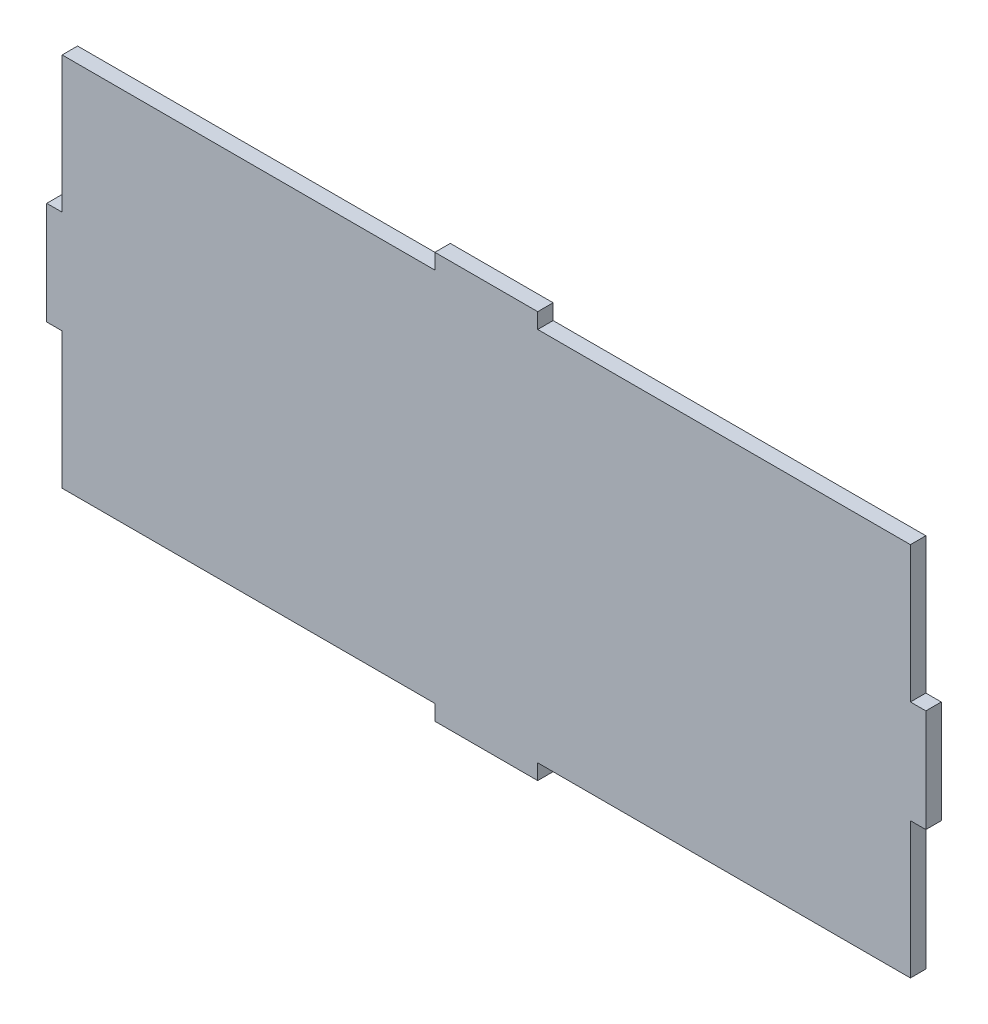
SolidWorks part; units mm, degrees
ref_plane "Plano frontal" through (0, 0, 0) normal (0, 0, 1) x (1, 0, 0)
ref_plane "Plano superior" through (0, 0, 0) normal (0, 1, 0) x (1, 0, 0)
ref_plane "Plano direito" through (0, 0, 0) normal (1, 0, 0) x (0, 0, -1)
sketch "Esboço1" plane through (0, 0, 0) normal (0, 0, 1) x (1, 0, 0)
  line L0 (-82.5, 36.5) -> (82.5, 36.5)
  line L1 (-82.5, 36.5) -> (-82.5, -36.5)
  line L2 (-82.5, -36.5) -> (82.5, -36.5)
  line L3 (82.5, 36.5) -> (82.5, -36.5)
  line L4 (-82.5, 10) -> (-85.5, 10)
  line L5 (-82.5, 10) -> (-82.5, -10)
  line L6 (-82.5, -10) -> (-85.5, -10)
  line L7 (-85.5, 10) -> (-85.5, -10)
  line L8 (-10, -36.5) -> (10, -36.5)
  line L9 (-10, -36.5) -> (-10, -39.5)
  line L10 (-10, -39.5) -> (10, -39.5)
  line L11 (10, -36.5) -> (10, -39.5)
  line L12 (10, 36.5) -> (-10, 36.5)
  line L13 (10, 36.5) -> (10, 39.5)
  line L14 (10, 39.5) -> (-10, 39.5)
  line L15 (-10, 36.5) -> (-10, 39.5)
  line L16 (82.5, 10) -> (85.5, 10)
  line L17 (82.5, 10) -> (82.5, -10)
  line L18 (82.5, -10) -> (85.5, -10)
  line L19 (85.5, 10) -> (85.5, -10)
extrude "Ressalto-extrusão1" add sketch "Esboço1" along normal blind 3 contours L3 L0 L1 L2 | L15 L0 L13 L14 | L7 L6 L5 L4 | L19 L18 L17 L16 | L10 L11 L8 L9
sketch "Logo-Maua" plane through (0, 0, 0) normal (0, 0, -1) x (-1, 0, 0)
  line L1 (-11.2957, 11.2957) -> (11.2957, 11.2957)
  line L2 (-11.2957, 11.2957) -> (-11.2957, -11.2957)
  line L3 (-11.2957, -11.2957) -> (11.2957, -11.2957)
  line L4 (11.2957, 11.2957) -> (11.2957, -11.2957)
  line L5 (-16.1458, 16.1458) -> (16.1458, 16.1458)
  line L6 (-16.1458, 16.1458) -> (-16.1458, -16.1458)
  line L7 (-16.1458, -16.1458) -> (16.1458, -16.1458)
  line L8 (16.1458, 16.1458) -> (16.1458, -16.1458)
  circle A0 centre (0, 0) radius 11.2957
  circle A1 centre (0, 0) radius 16.1458
